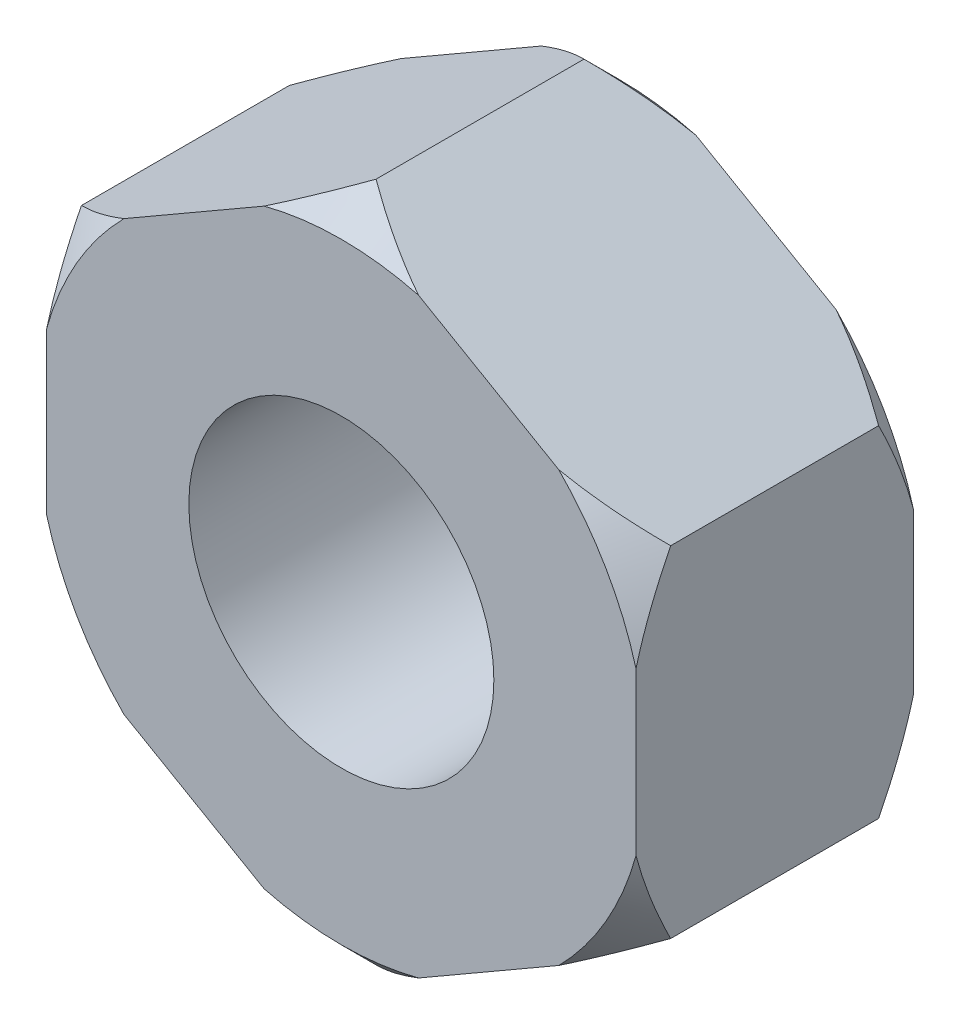
SolidWorks part; units mm, degrees
ref_plane "Front Plane" through (0, 0, 0) normal (0, 0, 1) x (1, 0, 0)
ref_plane "Top Plane" through (0, 0, 0) normal (0, 1, 0) x (1, 0, 0)
ref_plane "Right Plane" through (0, 0, 0) normal (1, 0, 0) x (0, 0, -1)
sketch "Sketch1" plane through (0, 0, 0) normal (0, 0, 1) x (1, 0, 0)
  line L1 (0, -9.815) -> (8.5, -4.9075)
  line L2 (8.5, -4.9075) -> (8.5, 4.9075)
  line L3 (8.5, 4.9075) -> (0, 9.815)
  line L4 (0, 9.815) -> (-8.5, 4.9075)
  line L5 (-8.5, 4.9075) -> (-8.5, -4.9075)
  line L6 (-8.5, -4.9075) -> (0, -9.815)
  circle A0 centre (0, 0) radius 8.5 construction
  dimension "D1" = 17
extrude "Boss-Extrude1" add sketch "Sketch1" along normal blind 8
sketch "Sketch3" plane through (0, 0, 0) normal (1, 0, 0) x (0, 0, -1)
  line L0 (-1, 9.815) -> (0, 8.815)
  line L1 (-8, 9.815) -> (0, 9.815) construction
  line L2 (0, 4.9075) -> (0, 9.815) construction
  line L3 (0, 8.815) -> (0, 9.815)
  line L4 (0, 9.815) -> (-1, 9.815)
  line L5 (0, 0) -> (3.2586, 0) construction
  line L6 (-4, 9.815) -> (-4, 3.9996) construction
  line L7 (-8, 8.815) -> (-8, 9.815)
  line L8 (-8, 9.815) -> (-7, 9.815)
  line L9 (-7, 9.815) -> (-8, 8.815)
  dimension "D1" = 1
  dimension "D2" = 1
revolve "Cut-Revolve8" cut sketch "Sketch3" angle 360 about L5
hole_wizard "M10x1.25 Tapped Hole1" positions "Sketch13" profile "Sketch14" tap size "M10x1.25" standard "ISO"
sketch "Sketch13" plane through (0, 0, 8) normal (0, 0, 1) x (1, 0, 0)
  point P0 (0, 0)
sketch "Sketch14" plane through (0, 0, 8) normal (1, 0, 0) x (0, -1, 0)
  line L0 (0, 0) -> (0, 26.3938)
  line L1 (0, 26.3938) -> (4.4, 23.75)
  line L2 (4.4, 23.75) -> (4.4, 0)
  line L5 (4.4, 0) -> (0, 0)
  line L10 (0, 26.3938) -> (-4.4, 23.75) construction
  line L11 (0, -6.35) -> (0, 107.95) construction
  dimension "Tap Drill Dia." = 8.8
  dimension "Tap Drill Depth" = 23.75
  dimension "Drill Angle" = 118
cosmetic thread "Hole Thread1" parameters "D1"=8, "D2"=10
